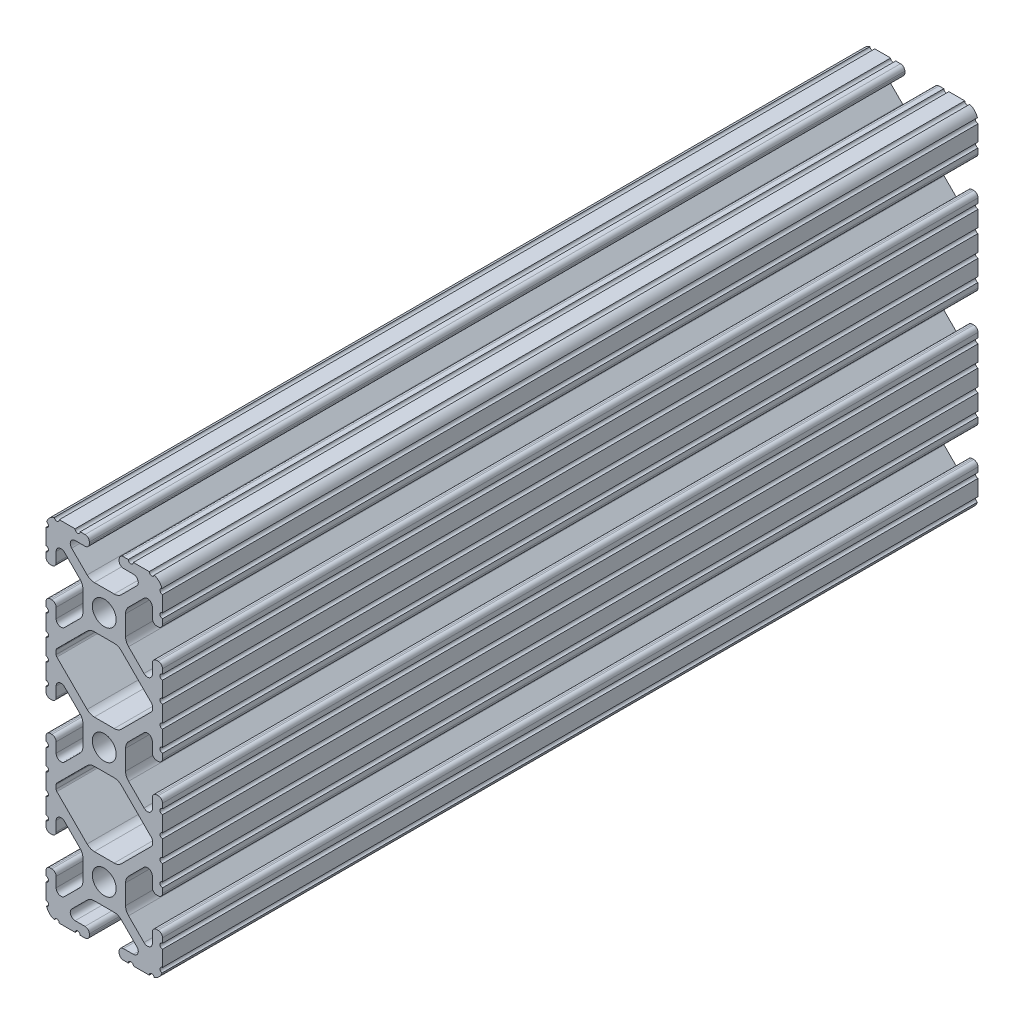
SolidWorks part; units mm, degrees
material "6061-T6 (SS)"
ref_plane "Front Plane" through (0, 0, 0) normal (0, 0, 1) x (1, 0, 0)
ref_plane "Top Plane" through (0, 0, 0) normal (0, 1, 0) x (1, 0, 0)
ref_plane "Right Plane" through (0, 0, 0) normal (1, 0, 0) x (0, 0, -1)
sketch "Sketch2" plane through (0, 0, 0) normal (0, 0, 1) x (1, 0, 0)
  line L0 (0, 38.1) -> (0, -38.1) construction
  line L1 (-12.7, 0) -> (12.7, 0) construction
  line L2 (3.2512, -38.1) -> (12.7, -38.1)
  line L3 (12.7, -38.1) -> (12.7, -28.6512)
  line L4 (3.2512, -38.1) -> (3.2512, -35.8902)
  line L5 (3.2512, -35.8902) -> (8.9276, -35.8902)
  line L6 (8.9276, -35.8902) -> (3.0856, -30.0482)
  line L7 (0, -25.4) -> (12.7, -38.1) construction
  line L8 (12.7, -28.6512) -> (10.4902, -28.6512)
  line L9 (10.4902, -28.6512) -> (10.4902, -34.3276)
  line L10 (10.4902, -34.3276) -> (4.6482, -28.4856)
  circle A0 centre (0, -25.4) radius 2.6035
  arc A1 (6.3485, -35.8902) -> (7.1039, -34.0665) centre (6.3485, -34.8219) ccw construction
  point P8 (0, -30.0482)
  dimension "Center Hole Diameter" = 5.207
  dimension "Rail Height" = 76.2
  dimension "Rail Width" = 25.4
  dimension "T-Slot Width" = 6.5024
  dimension "Slot Inner Width" = 14.8336
  dimension "Thickness" = 2.2098
  dimension "Slot Depth" = 5.842
  dimension "D1" = 2.2098
  dimension "D2" = 50.8
sketch "Sketch3" plane through (0, 0, 0) normal (1, 0, 0) x (0, 0, -1)
  line L0 (-152.4, -38.1) -> (152.4, -38.1) construction
  line L1 (-127, 0) -> (127, 0) construction
  dimension "D1" = 25.4
  dimension "Length" = 304.8
sketch "Sketch4" plane through (0, 0, 0) normal (0, 0, 1) x (1, 0, 0)
  line L0 (4.1904, -38.1) -> (10.1173, -38.1)
  line L1 (3.2512, -38.1) -> (12.7, -38.1) construction
  line L2 (3.2512, -38.1) -> (3.2512, -35.8902) construction
  line L3 (3.2512, -35.8902) -> (8.9276, -35.8902) construction
  line L4 (3.2512, -36.8294) -> (3.2512, -37.1608)
  line L5 (4.1904, -35.8902) -> (6.3485, -35.8902)
  line L6 (0, -30.0482) -> (2.164, -30.0482)
  line L7 (8.9276, -35.8902) -> (3.0856, -30.0482) construction
  line L8 (3.7373, -30.6999) -> (7.1039, -34.0665)
  line L9 (12.7, -38.1) -> (12.7, -28.6512) construction
  line L10 (10.4902, -34.3276) -> (4.6482, -28.4856) construction
  line L11 (10.4902, -28.6512) -> (10.4902, -34.3276) construction
  line L12 (10.4902, -31.7485) -> (10.4902, -29.5904)
  line L13 (12.7, -28.6512) -> (10.4902, -28.6512) construction
  line L14 (11.4294, -28.6512) -> (11.7608, -28.6512)
  line L15 (12.7, -29.5904) -> (12.7, -35.5173)
  line L16 (8.6665, -32.5039) -> (5.2999, -29.1373)
  line L17 (4.6482, -25.4) -> (4.6482, -27.564)
  line L19 (0, -30.0482) -> (0, -28.0035)
  line L20 (0, 38.1) -> (0, -38.1) construction
  line L21 (4.6482, -25.4) -> (2.6035, -25.4)
  arc A0 (3.2512, -37.1608) -> (4.1904, -38.1) centre (4.1904, -37.1608) ccw
  circle A1 centre (0, -25.4) radius 2.6035 construction
  arc A2 (3.2512, -36.8294) -> (4.1904, -35.8902) centre (4.1904, -36.8294) cw
  arc A3 (6.3485, -35.8902) -> (7.1039, -34.0665) centre (6.3485, -34.8219) ccw
  arc A4 (2.164, -30.0482) -> (3.7373, -30.6999) centre (2.164, -32.2732) cw
  arc A5 (10.1173, -38.1) -> (12.7, -35.5173) centre (10.1173, -35.5173) ccw
  arc A6 (8.6665, -32.5039) -> (10.4902, -31.7485) centre (9.4219, -31.7485) ccw
  arc A7 (10.4902, -29.5904) -> (11.4294, -28.6512) centre (11.4294, -29.5904) cw
  arc A8 (11.7608, -28.6512) -> (12.7, -29.5904) centre (11.7608, -29.5904) cw
  arc A9 (5.2999, -29.1373) -> (4.6482, -27.564) centre (6.8732, -27.564) cw
  arc A11 (0, -28.0035) -> (2.6035, -25.4) centre (0, -25.4) ccw
  dimension "D1" = 2.5827
  dimension "D2" = 2.225
  dimension "D3" = 0.9392
extrude "Boss-Extrude1" add sketch "Sketch4" along normal mid plane 177.8
sketch "Sketch5" plane through (0, 0, 0) normal (0, 0, 1) x (1, 0, 0)
  line L0 (3.2512, -38.1) -> (12.7, -38.1) construction
  line L1 (4.1904, -35.8902) -> (6.3485, -35.8902) construction
  line L3 (0, -25.4) -> (12.7, -38.1) construction
  line L4 (6.3485, -35.8902) -> (6.3485, -38.1) construction
  line L5 (8.9276, -35.8902) -> (3.0856, -30.0482) construction
  circle A0 centre (10.3562, -38.1) radius 0.5524
  circle A1 centre (5.796, -38.1) radius 0.5524
  circle A2 centre (12.7, -35.7562) radius 0.5525
  circle A3 centre (12.7, -31.196) radius 0.5525
  point P10 (5.2694, -35.8902)
  point P12 (9.4219, -31.7485)
  dimension "D1" = 1.1049
extrude "Cut-Extrude1" cut sketch "Sketch5" against normal through all both and the other way through all
mirror "Mirror1" about plane through (4.6482, -25.4, 88.9) normal (0, -1, 0) of bodies 137 134
sketch "Sketch6" plane through (0, 0, 0) normal (0, 0, 1) x (1, 0, 0)
  line L0 (12.7, -14.4914) -> (12.7, -12.7)
  line L1 (12.7, -12.7) -> (9.8037, -12.7)
  line L3 (9.8037, -12.7) -> (9.8037, -15.5963)
  line L4 (9.8037, -15.5963) -> (12.7, -15.5963)
  line L5 (6.3485, -12.7) -> (9.8037, -12.7) construction
  circle A0 centre (12.7, -15.0438) radius 0.5525 construction
  arc A1 (12.7, -14.4914) -> (12.7, -15.5963) centre (12.7, -15.0438) ccw
  arc A4 (9.8037, -12.7) -> (10.8954, -12.82) centre (10.3562, -12.7) ccw construction
extrude "Boss-Extrude2" add sketch "Sketch6" along normal mid plane 177.8
sketch "Sketch7" plane through (0, 0, 0) normal (0, 0, 1) x (1, 0, 0)
  line L0 (5.4206, -18.4168) -> (10.3284, -13.509)
  line L1 (3.7373, -20.1001) -> (7.1039, -16.7335) construction
  line L2 (10.4902, -13.1184) -> (10.4902, -12.7)
  line L3 (0, -12.7) -> (10.4902, -12.7)
  line L5 (0, -12.7) -> (5.4206, -18.4168)
  line L7 (0, 38.1) -> (0, -38.1) construction
  line L8 (6.3485, -12.7) -> (12.7, -12.7) construction
  arc A0 (10.3284, -13.509) -> (10.4902, -13.1184) centre (9.9377, -13.1184) ccw
  circle A3 centre (12.7, -15.0438) radius 0.5525 construction
extrude "Cut-Extrude2" cut sketch "Sketch7" against normal through all both and the other way through all
mirror "Mirror2" about plane through (4.1904, -12.7, 88.9) normal (0, -1, 0) of bodies 139 135
other "SurfaceCut1"
mirror "Mirror3" about plane through (0, 0, 0) normal (1, 0, 0) of bodies 142 136
mirror "Mirror4" about plane through (0, 0, 0) normal (0, 1, 0) of bodies 140
equation "\"D1@Boss-Extrude1\" = \"azimuth_vertictal_rail_length_short\""
equation "\"D1@Sketch2\"=\"Thickness@Sketch2\""
equation "\"D2@Sketch4\"=\"Slot Inner Width@Sketch2\"*0.15"
equation "\"D1@Sketch4\"=\"D3@Sketch4\"*2.75"
equation "\"D3@Sketch4\"=\"Thickness@Sketch2\"*0.425"
equation "\"D1@Sketch5\"= \"Thickness@Sketch2\" * 0.5"
equation "\"D1@Boss-Extrude2\" = \"azimuth_vertictal_rail_length_short\""
equation "\"azimuth_horizontal_rail_length\"=(\"altitude_horizontal_rail_length\"+6in-0.29in)"
equation "\"wall_screw_clearance_diameter\"=4.3mm"
equation "\"azimuth_vertictal_rail_length_short\"=(\"altitude_vertictal_rail_length\"-5in)"
equation "\"azimuth_vertictal_rail_length_long\"=(\"azimuth_vertictal_rail_length_short\"+4in)"
equation "\"altitude_horizontal_rail_length\"=10in"
equation "\"altitude_vertictal_rail_length\"=12in"
